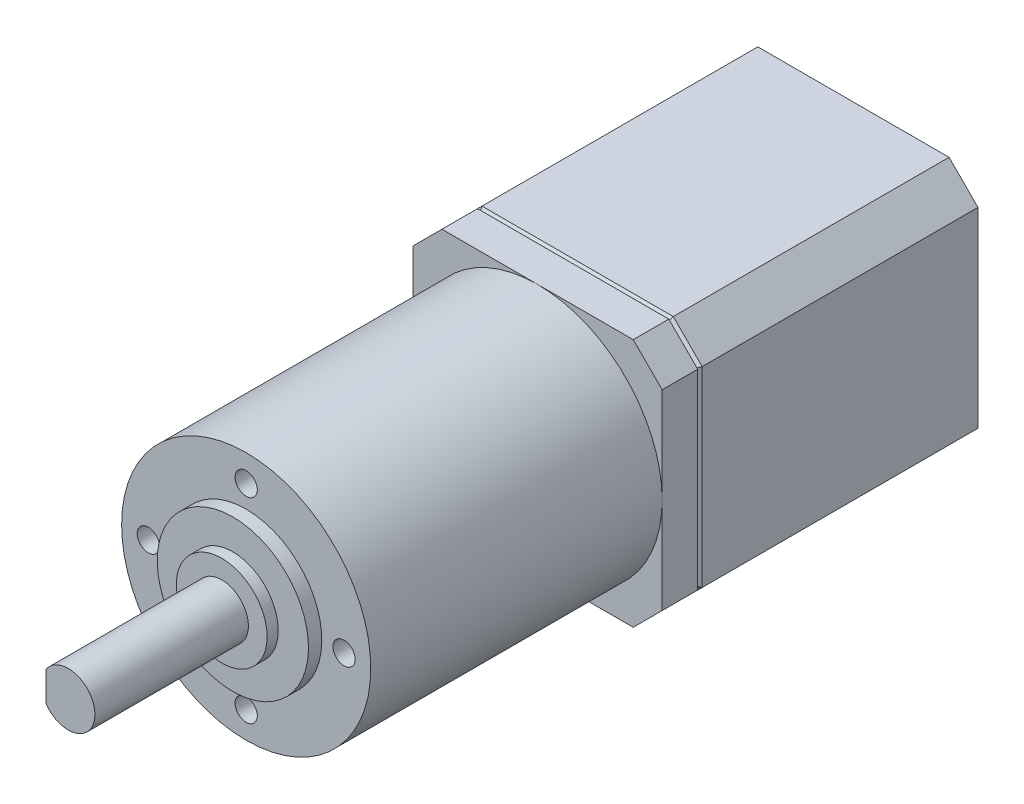
SolidWorks part; units mm, degrees
ref_plane "Front" through (0, 0, 0) normal (0, 0, 1) x (1, 0, 0)
ref_plane "Top" through (0, 0, 0) normal (0, 1, 0) x (1, 0, 0)
ref_plane "Right" through (0, 0, 0) normal (1, 0, 0) x (0, 0, -1)
sketch "Sketch1" plane through (0, 0, 0) normal (0, 0, 1) x (1, 0, 0)
  line L0 (-17.5226, -5.0947) -> (17.4774, -5.0947) construction
  line L1 (10.75, -14) -> (-10.75, -14)
  line L2 (14, -10.75) -> (14, 10.75)
  line L3 (10.75, 14) -> (-10.75, 14)
  line L4 (-14, -10.75) -> (-14, 10.75)
  line L5 (14, -14) -> (-14, 14) construction
  line L6 (14, 14) -> (-14, -14) construction
  line L7 (14, 10.75) -> (10.75, 14)
  line L8 (14, -10.75) -> (10.75, -14)
  line L9 (-10.75, -14) -> (-14, -10.75)
  line L10 (-10.75, 14) -> (-14, 10.75)
  point P0 (0, 0)
  dimension "D1" = 28
  dimension "D2" = 35
  dimension "D3" = 3.25
  dimension "D4" = 3.25
  dimension "D6" = 28
extrude "Boss-Extrude1" add sketch "Sketch1" along normal blind 31.5
ref_plane "Plane1" through (0, 0, 0) normal (1, 0, 0) x (0, 0, -1)
sketch "Sketch2" plane through (0, 0, 0) normal (1, 0, 0) x (0, 0, -1)
  line L0 (-79.6242, -0.2515) -> (-61.6242, -0.2515) construction
  dimension "D1" = 18
sketch "Sketch3" plane through (0, 0, 31.5) normal (0, 0, 1) x (1, 0, 0)
  line L8 (14, 10.75) -> (10.75, 14)
  line L9 (10.75, 14) -> (-10.75, 14)
  line L10 (-10.75, 14) -> (-14, 10.75)
  line L11 (-14, 10.75) -> (-14, -10.75)
  line L12 (-14, -10.75) -> (-10.75, -14)
  line L13 (-10.75, -14) -> (10.75, -14)
  line L14 (10.75, -14) -> (14, -10.75)
  line L15 (14, -10.75) -> (14, 10.75)
  line L16 (14, 10.75) -> (10.75, 14)
  line L17 (10.75, 14) -> (-10.75, 14)
  line L18 (-10.75, 14) -> (-14, 10.75)
  line L19 (-14, 10.75) -> (-14, -10.75)
  line L20 (-14, -10.75) -> (-10.75, -14)
  line L21 (-10.75, -14) -> (10.75, -14)
  line L22 (10.75, -14) -> (14, -10.75)
  line L23 (14, -10.75) -> (14, 10.75)
  dimension "D1" = 0
extrude "Boss-Extrude2" add sketch "Sketch3" along normal blind 4 separate body
chamfer "Chamfer1" distance 0.5 angle 45 8 edges at (0, 14, 31.5) (-12.375, 12.375, 31.5) (-14, 0, 31.5) (-12.375, -12.375, 31.5) (0, -14, 31.5) (12.375, -12.375, 31.5) (14, 0, 31.5) (12.375, 12.375, 31.5)
sketch "Sketch4" plane through (0, 0, 0) normal (1, 0, 0) x (0, 0, -1)
  line L0 (-35.5, 0) -> (-88.25, 0) construction
  line L1 (-35.5, -10.75) -> (-35.5, 10.75) construction
  line L2 (-88.25, 0) -> (-88.25, 3)
  line L3 (-88.25, 3) -> (-69.75, 3)
  line L4 (-69.75, 3) -> (-69.75, 8.5)
  line L5 (-75.9513, 30.812) -> (-39.8513, 30.812) construction
  line L7 (-69.75, 8.5) -> (-68.25, 8.5)
  line L8 (-68.25, 8.5) -> (-68.25, 14)
  line L9 (-68.25, 14) -> (-35.5, 14)
  line L11 (-35.5, 14) -> (-35.5, 0)
  line L12 (-35.5, 0) -> (-88.25, 0)
  dimension "D1" = 32.75
  dimension "D2" = 6
  dimension "D3" = 17
  dimension "D4" = 36.1
  dimension "D5" = 20
  dimension "D6" = 28
  dimension "D8" = 1.5
revolve "Revolve1" add sketch "Sketch4" angle 360 about L0
hole_wizard "M3x0.5 Tapped Hole1" positions "Sketch6" profile "Sketch7" tap size "M3x0.5" standard "ANSI Metric"
sketch "Sketch6" plane through (0, 0, 68.25) normal (0, 0, 1) x (1, 0, 0)
  line L0 (0, 0) -> (0, 11) construction
  line L3 (0, 0) -> (11, 0) construction
  line L6 (0, 0) -> (0, -11) construction
  line L9 (0, 0) -> (-11, 0) construction
  point P0 (0, 11)
  point P11 (11, 0)
  point P17 (0, -11)
  point P23 (-11, 0)
  dimension "D1" = 11
sketch "Sketch7" plane through (0, 11, 68.25) normal (1, 0, 0) x (0, -1, 0)
  line L0 (0, 0) -> (0, 5.7511)
  line L1 (0, 5.7511) -> (1.25, 5)
  line L2 (1.25, 5) -> (1.25, 0)
  line L5 (1.25, 0) -> (0, 0)
  line L10 (0, 5.7511) -> (-1.25, 5) construction
  line L11 (0, -6.35) -> (0, 107.95) construction
  dimension "Tap Drill Dia." = 2.5
  dimension "Tap Drill Depth" = 5
  dimension "Drill Angle" = 118
cosmetic thread "Hole Thread1" parameters "D1"=6, "D2"=3
cosmetic thread "Hole Thread2" parameters "D1"=6, "D2"=3
cosmetic thread "Hole Thread3" parameters "D1"=6, "D2"=3
cosmetic thread "Hole Thread4" parameters "D1"=6, "D2"=3
sketch "Sketch8" plane through (0, 0, 69.75) normal (0, 0, 1) x (1, 0, 0)
  circle A0 centre (0, 0) radius 5.1
  circle A1 centre (0, 0) radius 3 construction
  circle A2 centre (0, 0) radius 3
  dimension "D1" = 10.2
extrude "Boss-Extrude3" add sketch "Sketch8" along normal blind 1.25
sketch "Sketch9" plane through (0, 0, 88.25) normal (0, 0, 1) x (1, 0, 0)
  line L0 (-2.5, 1.6583) -> (-2.5, -1.6583)
  line L1 (-2.5, 0) -> (0, 0) construction
  arc A0 (-2.5, 1.6583) -> (-2.5, -1.6583) centre (0, 0) ccw
  circle A1 centre (0, 0) radius 3 construction
  point P6 (-3, 0)
  dimension "D1" = 0.5
extrude "Cut-Extrude1" cut sketch "Sketch9" against normal blind 15
equation "\"D6@Sketch1\"=\"D1@Sketch1\""
